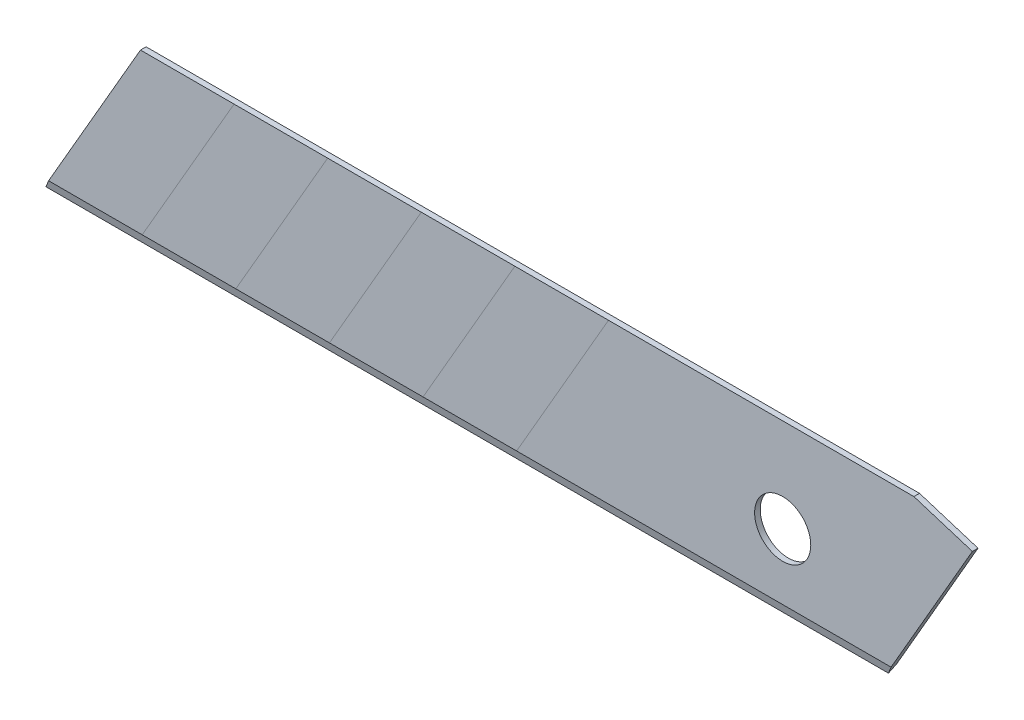
SolidWorks part; units mm, degrees
material "1.0715 (11SMn30)"
ref_plane "前视基准面" through (0, 0, 0) normal (0, 0, 1) x (1, 0, 0)
ref_plane "上视基准面" through (0, 0, 0) normal (0, 1, 0) x (1, 0, 0)
ref_plane "右视基准面" through (0, 0, 0) normal (1, 0, 0) x (0, 0, -1)
sketch "草图1" plane through (0, 0, 0) normal (0, 0, 1) x (1, 0, 0)
  line L0 (0, 10.6028) -> (0, -10.9724) construction
  line L1 (-16.8166, 0) -> (14.4142, 0) construction
  line L2 (-74.5, -4) -> (5.5, -4)
  line L3 (-74.5, -4) -> (-69.8673, 4.024)
  line L4 (5.5, -4) -> (10.1327, 4.024)
  line L5 (-65.9879, 5) -> (7.0091, 5)
  line L6 (7.0091, 5) -> (10.1327, 4.024)
  circle A0 centre (0, 0) radius 1.5
  arc A1 (-69.8673, 4.024) -> (-65.9879, 5) centre (-70.7283, 15.6446) ccw
  dimension "D1" = 3
  dimension "D2" = 9
  dimension "D3" = 80
  dimension "D4" = 5
  dimension "D5" = 60
  dimension "D6" = 5.5
extrude "凸台-拉伸1" add sketch "草图1" along normal mid plane 0.3
sketch "草图3" plane through (0, 0, 0) normal (1, 0, 0) x (0, 0, -1)
  line L0 (0, 6.5194) -> (0, -8.4917) construction
  line L1 (0, -4) -> (-0.15, -3.5)
  line L2 (-0.15, 4.024) -> (-0.15, -4) construction
  line L3 (0, -4) -> (0.15, -3.5)
  line L4 (0.15, 4.024) -> (0.15, -4) construction
  line L5 (-0.15, -4) -> (0.15, -4) construction
  line L6 (0.15, -3.5) -> (0.6027, -4.3305)
  line L7 (0.6027, -4.3305) -> (-0.7473, -4.3305)
  line L8 (-0.7473, -4.3305) -> (-0.15, -3.5)
  line L9 (0.15, -4) -> (0.15, 4.024) construction
  dimension "D1" = 0.5
extrude "切除-拉伸1" cut sketch "草图3" against normal blind 80.3 and the other way blind 13
sketch "草图5" plane through (0, 0, 0.15) normal (0, 0, 1) x (1, 0, 0)
  line L1 (-64.3038, 5) -> (-69.2113, -3.5)
  line L2 (-59.3038, 5) -> (-64.2113, -3.5)
  line L3 (-54.3038, 5) -> (-59.2113, -3.5)
  line L4 (-49.3038, 5) -> (-54.2113, -3.5)
  line L5 (-44.3038, 5) -> (-49.2113, -3.5)
  line L6 (-39.3038, 5) -> (-44.2113, -3.5)
  line L7 (-34.3038, 5) -> (-39.2113, -3.5)
  line L8 (-29.3038, 5) -> (-34.2113, -3.5)
  line L9 (-24.3038, 5) -> (-29.2113, -3.5)
  line L10 (-19.3038, 5) -> (-24.2113, -3.5)
  line L11 (-14.3038, 5) -> (-19.2113, -3.5)
  line L12 (-9.3038, 5) -> (-14.2113, -3.5)
  line L14 (7.0091, 5) -> (-65.9879, 5) construction
  line L16 (5.7887, -3.5) -> (-74.2113, -3.5) construction
split line "分割线2"
sketch "草图6" plane through (0, 0, -0.15) normal (0, 0, -1) x (-1, 0, 0)
  line L1 (69.2113, -3.5) -> (64.3038, 5)
  line L2 (64.2113, -3.5) -> (59.3038, 5)
  line L3 (59.2113, -3.5) -> (54.3038, 5)
  line L4 (54.2113, -3.5) -> (49.3038, 5)
  line L5 (49.2113, -3.5) -> (44.3038, 5)
  line L6 (44.2113, -3.5) -> (39.3038, 5)
  line L7 (39.2113, -3.5) -> (34.3038, 5)
  line L8 (34.2113, -3.5) -> (29.3038, 5)
  line L9 (29.2113, -3.5) -> (24.3038, 5)
  line L10 (24.2113, -3.5) -> (19.3038, 5)
  line L11 (19.2113, -3.5) -> (14.3038, 5)
  line L12 (14.2113, -3.5) -> (9.3038, 5)
  line L15 (-5.7887, -3.5) -> (74.2113, -3.5) construction
split line "分割线3"
sketch "草图7" plane through (0, 0, 0.15) normal (0, 0, 1) x (1, 0, 0)
  line L0 (-30.4764, 11.6294) -> (-39.5, -4)
  line L2 (-39.5, -4) -> (-74.5, -4)
  line L3 (-74.5, -4) -> (-62.9538, 15.9985)
  line L4 (-62.9538, 15.9985) -> (-30.4764, 11.6294)
  line L6 (-39.2113, -3.5) -> (-34.3038, 5) construction
extrude "切除-拉伸2" cut sketch "草图7" against normal through all
